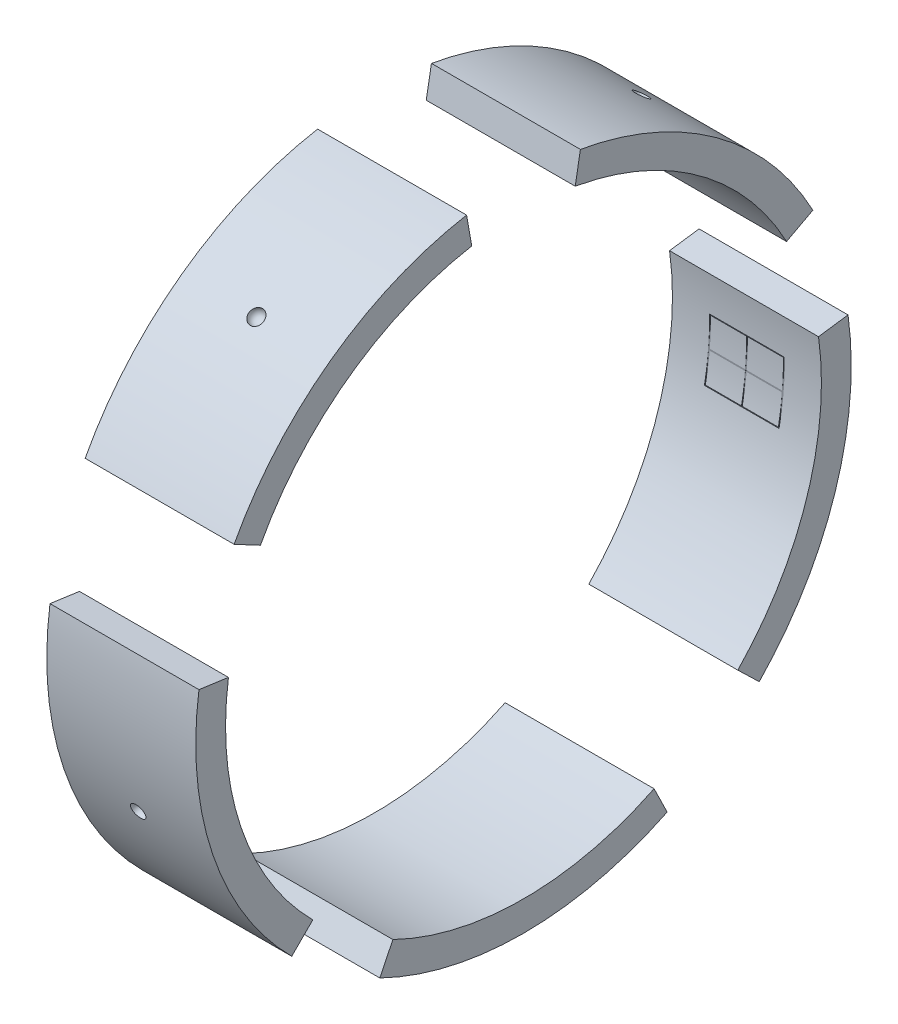
SolidWorks part; units mm, degrees
ref_plane "Front Plane" through (0, 0, 0) normal (0, 0, 1) x (1, 0, 0)
ref_plane "Top Plane" through (0, 0, 0) normal (0, 1, 0) x (1, 0, 0)
ref_plane "Right Plane" through (0, 0, 0) normal (1, 0, 0) x (0, 0, -1)
sketch "Sketch1" plane through (0, 0, 0) normal (1, 0, 0) x (0, 0, -1)
  line L1 (87.6742, -179.7588) -> (96.4417, -197.7347)
  line L2 (143.868, -138.9317) -> (158.2548, -152.8248)
  line L4 (198.0536, 27.8346) -> (217.859, 30.6181)
  line L5 (176.5895, 93.8943) -> (194.2485, 103.2837)
  line L7 (34.7296, 196.9616) -> (38.2026, 216.6577)
  line L8 (-34.7296, 196.9616) -> (-38.2026, 216.6577)
  line L10 (-176.5895, 93.8943) -> (-194.2485, 103.2837)
  line L11 (-198.0536, 27.8346) -> (-217.859, 30.6181)
  line L13 (-141.4214, -141.4214) -> (-155.5635, -155.5635)
  line L14 (-87.6742, -179.7588) -> (-96.4417, -197.7347)
  arc A0 (143.868, -138.9317) -> (198.0536, 27.8346) centre (0, 0) ccw
  arc A1 (158.2548, -152.8248) -> (217.859, 30.6181) centre (0, 0) ccw
  arc A2 (194.2485, 103.2837) -> (38.2026, 216.6577) centre (0, 0) ccw
  arc A3 (176.5895, 93.8943) -> (34.7296, 196.9616) centre (0, 0) ccw
  arc A4 (-38.2026, 216.6577) -> (-194.2485, 103.2837) centre (0, 0) ccw
  arc A5 (-34.7296, 196.9616) -> (-176.5895, 93.8943) centre (0, 0) ccw
  arc A6 (-198.0536, 27.8346) -> (-141.4214, -141.4214) centre (0, 0) ccw
  arc A7 (-217.859, 30.6181) -> (-155.5635, -155.5635) centre (0, 0) ccw
  arc A8 (-87.6742, -179.7588) -> (87.6742, -179.7588) centre (0, 0) ccw
  arc A9 (-96.4417, -197.7347) -> (96.4417, -197.7347) centre (0, 0) ccw
  point P8 (0, -220)
  point P11 (-208.6312, -69.807)
  point P14 (-129.3128, 177.9837)
  point P17 (129.3128, 177.9837)
  point P19 (209.2324, -67.9837)
  point P26 (87.6742, -179.7588)
  point P27 (143.868, -138.9317)
  point P29 (198.0536, 27.8346)
  point P30 (176.5895, 93.8943)
  point P32 (34.7296, 196.9616)
  point P33 (-34.7296, 196.9616)
extrude "Boss-Extrude1" add sketch "Sketch1" along normal blind 100
ref_plane "Plane1" through (0, 177.9837, 129.3128) normal (0, 0.809, 0.5878) x (1, 0, 0)
ref_plane "Plane2" through (0, -69.807, 208.6312) normal (0, -0.3173, 0.9483) x (1, 0, 0)
ref_plane "Plane3" through (0, -67.9837, -209.2324) normal (0, -0.309, -0.9511) x (-1, 0, 0)
ref_plane "Plane4" through (0, -220, 0) normal (0, -1, 0) x (-1, 0, 0)
ref_plane "Plane5" through (0, 177.9837, -129.3128) normal (0, 0.809, -0.5878) x (1, 0, 0)
sketch "Sketch2" plane through (0, 177.9837, 129.3128) normal (0, 0.809, 0.5878) x (1, 0, 0)
  line L0 (45, 0) -> (55, 0)
  arc A0 (55, 0) -> (45, 0) centre (50, 0) ccw
  point P6 (50, 0)
sketch "Sketch4" plane through (0, 177.9837, -129.3128) normal (0, 0.809, -0.5878) x (1, 0, 0)
  line L0 (45, 0) -> (55, 0)
  arc A0 (55, 0) -> (45, 0) centre (50, 0) ccw
  point P6 (50, 0)
sketch "Sketch5" plane through (0, -67.9837, -209.2324) normal (0, -0.309, -0.9511) x (-1, 0, 0)
  line L0 (-55, 0) -> (-45, 0)
  arc A0 (-45, 0) -> (-55, 0) centre (-50, 0) ccw
  point P5 (-50, 0)
sketch "Sketch6" plane through (0, -220, 0) normal (0, -1, 0) x (-1, 0, 0)
  line L0 (-55, 0) -> (-45, 0)
  arc A0 (-45, 0) -> (-55, 0) centre (-50, 0) cw
  point P5 (-50, 0)
sketch "Sketch7" plane through (0, -69.807, 208.6312) normal (0, -0.3173, 0.9483) x (1, 0, 0)
  line L0 (45, 0) -> (55, 0)
  arc A0 (55, 0) -> (45, 0) centre (50, 0) ccw
  point P5 (50, 0)
revolve "Cut-Revolve1" cut sketch "Sketch2" angle 360 about L0
revolve "Cut-Revolve2" cut sketch "Sketch4" angle 360 about L0
revolve "Cut-Revolve3" cut sketch "Sketch5" angle 360 about L0
revolve "Cut-Revolve4" cut sketch "Sketch6" angle 360 about L0
revolve "Cut-Revolve5" cut sketch "Sketch7" angle 360 about L0
ref_plane "Plane6" through (-10, 0, 0) normal (-1, 0, 0) x (0, 0, 1)
sketch "Sketch8" plane through (-10, 0, 0) normal (-1, 0, 0) x (0, 0, 1)
  line L0 (-129.3128, 177.9837) -> (-117.5571, 161.8034)
  line L1 (117.5571, 161.8034) -> (129.3128, 177.9837)
  line L2 (-190.2113, -61.8034) -> (-209.2324, -67.9837)
  line L3 (190.2113, -61.8034) -> (209.2324, -67.9837)
  line L4 (0, -200) -> (0, -220)
  line L5 (-150.9419, 131.2118) -> (-166.0361, 144.333)
  line L6 (-78.1462, 184.101) -> (-85.9608, 202.5111)
  line L7 (150.9419, 131.2118) -> (166.0361, 144.333)
  line L8 (78.1462, 184.101) -> (85.9608, 202.5111)
  line L9 (199.3447, -16.1766) -> (219.4045, -16.1766)
  line L10 (172.2044, -100.0777) -> (190.2113, -110.5426)
  line L11 (44.9902, -194.874) -> (49.4892, -214.3614)
  line L12 (-44.9902, -194.874) -> (-49.4892, -214.3614)
  line L13 (-171.4335, -103.0076) -> (-188.5768, -113.3084)
  line L14 (-199.2389, -17.4311) -> (-219.1628, -19.1743)
  arc A5 (-87.6742, -179.7588) -> (87.6742, -179.7588) centre (0, 0) ccw construction
  arc A6 (-198.0536, 27.8346) -> (-143.868, -138.9317) centre (0, 0) ccw construction
  arc A7 (-34.7296, 196.9616) -> (-176.5895, 93.8943) centre (0, 0) ccw construction
  arc A8 (176.5895, 93.8943) -> (34.7296, 196.9616) centre (0, 0) ccw construction
  arc A9 (141.4214, -141.4214) -> (198.0536, 27.8346) centre (0, 0) ccw construction
  circle A10 centre (0, 0) radius 220
  point P0 (-123.4349, 169.8936)
  point P1 (123.4349, 169.8936)
  point P3 (199.7219, -64.8936)
  point P5 (-117.5571, 161.8034)
  point P10 (117.5571, 161.8034)
  point P11 (190.2113, -61.8034)
  point P12 (0, -200)
  point P13 (-190.2113, -61.8034)
  point P19 (0, -210)
  point P20 (-199.7219, -64.8936)
  point P27 (-44.9902, -194.874)
  point P44 (-158.489, 137.7724)
  point P45 (-82.0535, 193.306)
  point P46 (82.0535, 193.306)
  point P47 (158.489, 137.7724)
  point P48 (209.3746, -16.1766)
  point P49 (44.9902, -194.874)
  point P53 (172.2044, -100.0777)
  point P54 (-171.4335, -103.0076)
  point P55 (-199.2389, -17.4311)
  point P59 (-150.9419, 131.2118)
  point P60 (-78.1462, 184.101)
  point P64 (78.1462, 184.101)
  point P65 (150.9419, 131.2118)
  point P69 (199.3447, -16.1766)
  point P70 (181.2078, -105.3102)
  point P74 (47.2397, -204.6177)
  point P75 (-47.2397, -204.6177)
  point P76 (-180.0051, -108.158)
  point P77 (-209.2009, -18.3027)
hole_wizard "1/2-13 Tapped Hole1" positions "3DSketch1" profile "Sketch9" tap size "1/2-13" standard "ANSI Inch"
sketch3d "3DSketch1"
  line L0 (-10, 184.101, 78.1462) -> (-10, 202.5111, 85.9608) construction
  point P0 (-10, -108.158, -180.0051)
  point P3 (-10, -18.3027, -209.2009)
  point P6 (-10, -204.6177, -47.2397)
  point P9 (-10, -204.6177, 47.2397)
  point P12 (-10, -105.3102, 181.2078)
  point P15 (-10, -16.1766, 209.3746)
  point P18 (-10, 137.7724, 158.489)
  point P21 (-10, 193.306, 82.0535)
  point P25 (-10, 137.7724, -158.489)
  point P28 (-10, 193.306, -82.0535)
sketch "Sketch9" plane through (-10, -108.158, -180.0051) normal (0, 1, 0) x (0, 0, 1)
  line L0 (0, 0) -> (0, 69.1195)
  line L1 (0, 69.1195) -> (5.3581, 65.9)
  line L2 (5.3581, 65.9) -> (5.3581, 0)
  line L5 (5.3581, 0) -> (0, 0)
  line L10 (0, 69.1195) -> (-5.3581, 65.9) construction
  line L11 (0, -6.35) -> (0, 107.95) construction
  dimension "Tap Drill Dia." = 10.7163
  dimension "Tap Drill Depth" = 65.9
  dimension "Drill Angle" = 118
ref_plane "Plane7" through (-10, -17.4311, -199.2389) normal (0, 0.0872, 0.9962) x (1, 0, 0)
sketch "Sketch10" plane through (-10, -17.4311, -199.2389) normal (0, 0.0872, 0.9962) x (1, 0, 0)
  line L0 (0, 0) -> (110, 0)
  line L1 (110, -125.8641) -> (110, 44.9902) construction
  line L2 (0, -92.0579) -> (110, -92.0579)
  line L4 (34.9502, -19.9376) -> (85.0498, -19.9376)
  line L5 (34.9502, -19.9376) -> (34.9502, 19.9376)
  line L6 (34.9502, 19.9376) -> (85.0498, 19.9376)
  line L7 (85.0498, -19.9376) -> (85.0498, 19.9376)
  line L8 (34.9502, -19.9376) -> (85.0498, 19.9376) construction
  line L9 (34.9502, 19.9376) -> (85.0498, -19.9376) construction
  line L10 (35.5, -19.5) -> (84.5, -19.5)
  line L11 (35.5, -19.5) -> (35.5, 19.5)
  line L12 (35.5, 19.5) -> (84.5, 19.5)
  line L13 (84.5, -19.5) -> (84.5, 19.5)
  line L14 (35.5, -19.5) -> (84.5, 19.5) construction
  line L15 (35.5, 19.5) -> (84.5, -19.5) construction
  point P8 (60, 0)
  point P9 (50, -92.0579)
  point P10 (60, 0)
  point P15 (60, 0)
extrude "Cut-Extrude6" cut sketch "Sketch10" along normal blind 22 contours L5 L6 L7 L4 | L11 L12 L13 L10
sketch "Sketch11" plane through (-10, -17.4311, -199.2389) normal (0, 0.0872, 0.9962) x (1, 0, 0)
  line L0 (35.5, 0.25) -> (59.75, 0.25)
  line L1 (35.5, 19.5) -> (84.5, 19.5) construction
  line L3 (60.25, -0.25) -> (60.25, -19.5)
  line L4 (84.5, -19.5) -> (84.5, 0) construction
  line L5 (60.25, 19.5) -> (60.25, 0.25)
  line L6 (35.5, -19.5) -> (84.5, -19.5) construction
  line L7 (59.75, 19.5) -> (59.75, 0.25)
  line L8 (35.5, 19.5) -> (84.5, 19.5) construction
  line L10 (35.5, 19.5) -> (35.5, 0) construction
  line L11 (84.5, 0) -> (84.5, 19.5) construction
  line L12 (84.5, -0.25) -> (60.25, -0.25)
  line L13 (35.5, -19.5) -> (35.5, 0) construction
  line L14 (60.25, 0.25) -> (84.5, 0.25)
  line L15 (59.75, -0.25) -> (59.75, -19.5)
  line L16 (59.75, -0.25) -> (35.5, -0.25)
  line L17 (84.5, 0.25) -> (84.5, -0.25)
  line L18 (60.25, 19.5) -> (59.75, 19.5)
  line L19 (35.5, 0.25) -> (35.5, -0.25)
  line L20 (59.75, -19.5) -> (60.25, -19.5)
  point P28 (60, 0)
  dimension "D3" = 0.5
extrude "Cut-Extrude7" cut sketch "Sketch11" along normal blind 28 contours L5 L14 L17 L12 L3 L20 L15 L16 L19 L0 L7 L18
ref_plane "Plane8" through (0, -17.4311, -199.2389) normal (0, 0.0872, 0.9962) x (1, 0, 0)
hole_wizard "#78 (0.016) Diameter Hole2" positions "3DSketch3" profile "Sketch16" hole size "#78" standard "ANSI Inch"
sketch3d "3DSketch3"
  point P0 (50.0003, -17.4228, -199.2397)
sketch "Sketch16" plane through (50.0003, -17.4228, -199.2397) normal (1, 0, 0) x (0, -0.9962, 0.0872)
  line L0 (0, 0) -> (0, 10.1221)
  line L1 (0, 10.1221) -> (0.2032, 10)
  line L2 (0.2032, 10) -> (0.2032, 0)
  line L5 (0.2032, 0) -> (0, 0)
  line L10 (0, 10.1221) -> (-0.2032, 10) construction
  line L11 (0, -6.35) -> (0, 107.95) construction
  dimension "Hole Dia." = 0.4064
  dimension "Hole Depth" = 10
  dimension "Drill Angle" = 118
ref_plane "Plane9" through (-10, -103.0076, -171.4335) normal (0, 0.515, 0.8572) x (1, 0, 0)
